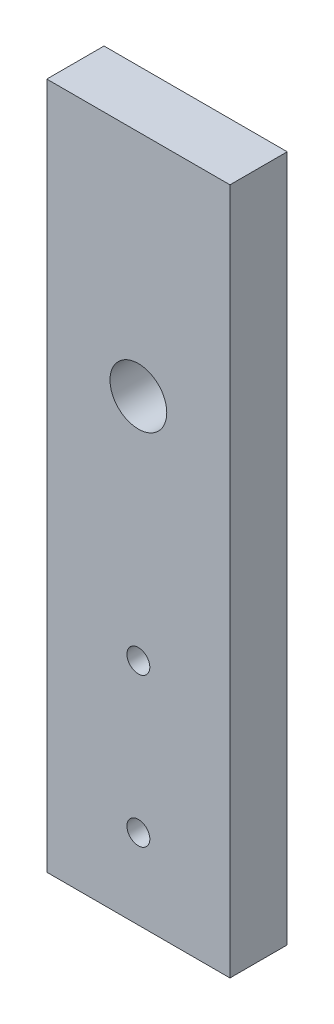
SolidWorks part; units mm, degrees
material "Mahogany"
ref_plane "Front Plane" through (0, 0, 0) normal (0, 0, 1) x (1, 0, 0)
ref_plane "Top Plane" through (0, 0, 0) normal (0, 1, 0) x (1, 0, 0)
ref_plane "Right Plane" through (0, 0, 0) normal (1, 0, 0) x (0, 0, -1)
sketch "Sketch1" plane through (0, 0, 0) normal (0, 0, 1) x (1, 0, 0)
  line L0 (-40, 300) -> (-40, 200) construction
  line L1 (0, 0) -> (-80, 0)
  line L2 (0, 0) -> (0, 300)
  line L3 (0, 300) -> (-80, 300)
  line L4 (-80, 0) -> (-80, 300)
  line L5 (-40, 0) -> (-40, 35) construction
  line L6 (-40, 200) -> (-40, 100) construction
  line L7 (-40, 100) -> (-40, 35) construction
  circle A0 centre (-40, 200) radius 12.4
  circle A1 centre (-40, 35) radius 5
  circle A2 centre (-40, 100) radius 5
  dimension "D3" = 24.8
  dimension "D5" = 100
  dimension "D7" = 10
  dimension "D8" = 10
  dimension "D1" = 80
  dimension "D2" = 300
  dimension "D4" = 100
  dimension "D6" = 65
extrude "Boss-Extrude2" add sketch "Sketch1" against normal blind 25
